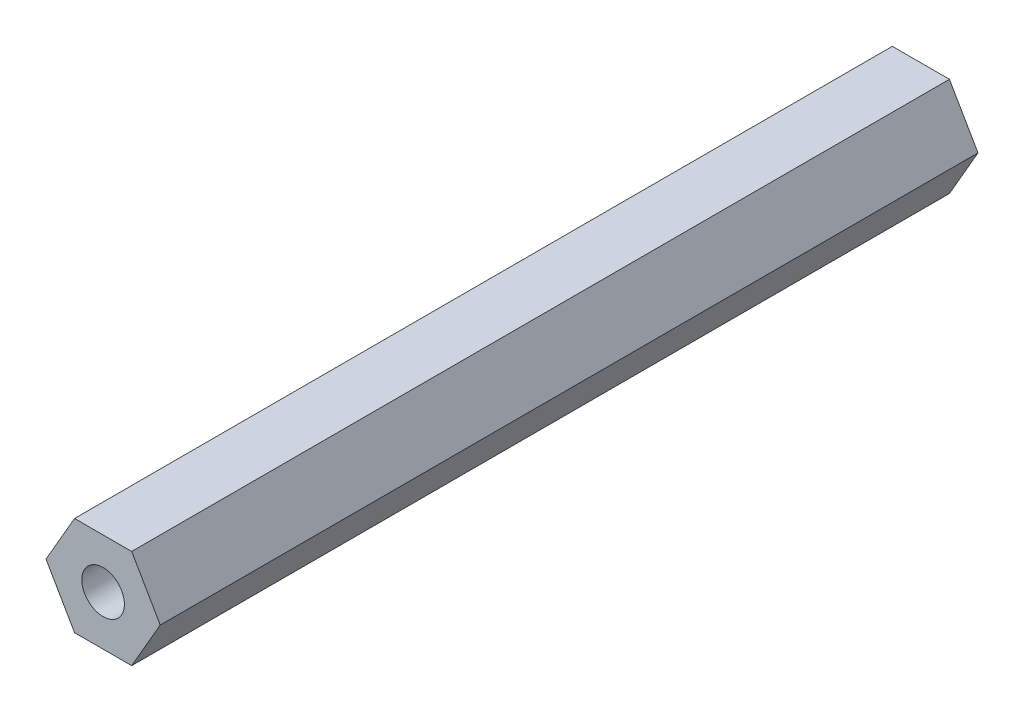
SolidWorks part; units mm, degrees
material "Latón"
ref_plane "Alzado" through (0, 0, 0) normal (0, 0, 1) x (1, 0, 0)
ref_plane "Planta" through (0, 0, 0) normal (0, 1, 0) x (1, 0, 0)
ref_plane "Vista lateral" through (0, 0, 0) normal (1, 0, 0) x (0, 0, -1)
sketch "Croquis1" plane through (0, 0, 0) normal (0, 0, 1) x (1, 0, 0)
  line L1 (4.5611, 0) -> (2.2805, 3.95)
  line L2 (2.2805, 3.95) -> (-2.2805, 3.95)
  line L3 (-2.2805, 3.95) -> (-4.5611, 0)
  line L4 (-4.5611, 0) -> (-2.2805, -3.95)
  line L5 (-2.2805, -3.95) -> (2.2805, -3.95)
  line L6 (2.2805, -3.95) -> (4.5611, 0)
  circle A0 centre (0, 0) radius 3.95 construction
  dimension "D1" = 7.9
extrude "Saliente-Extruir1" add sketch "Croquis1" along normal blind 65.3 contours L3 L4 L5 L6 L1 L2
sketch "Croquis2" plane through (0, 0, 65.3) normal (0, 0, 1) x (1, 0, 0)
  circle A0 centre (0, 0) radius 1.7
  dimension "D1" = 3.4
extrude "Cortar-Extruir1" cut sketch "Croquis2" against normal blind 65.3
